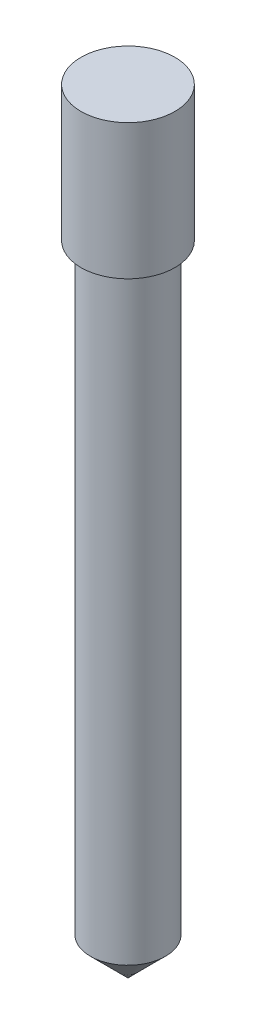
SolidWorks part; units mm, degrees
ref_plane "Front Plane" through (0, 0, 0) normal (0, 0, 1) x (1, 0, 0)
ref_plane "Top Plane" through (0, 0, 0) normal (0, 1, 0) x (1, 0, 0)
ref_plane "Right Plane" through (0, 0, 0) normal (1, 0, 0) x (0, 0, -1)
sketch "Sketch1" plane through (0, 0, 0) normal (0, 1, 0) x (1, 0, 0)
  circle A0 centre (0, 0) radius 5
  dimension "D1" = 10
extrude "Boss-Extrude1" add sketch "Sketch1" along normal blind 85
chamfer "Chamfer1" distance 5 angle 45 1 edges at (0, 0, 5)
sketch "Sketch2" plane through (0, 85, 0) normal (0, 1, 0) x (1, 0, 0)
  circle A1 centre (0, 0) radius 6.25
  point P5 (0, -4.85)
  dimension "D1" = 12.5
extrude "Boss-Extrude2" add sketch "Sketch2" along normal blind 18
